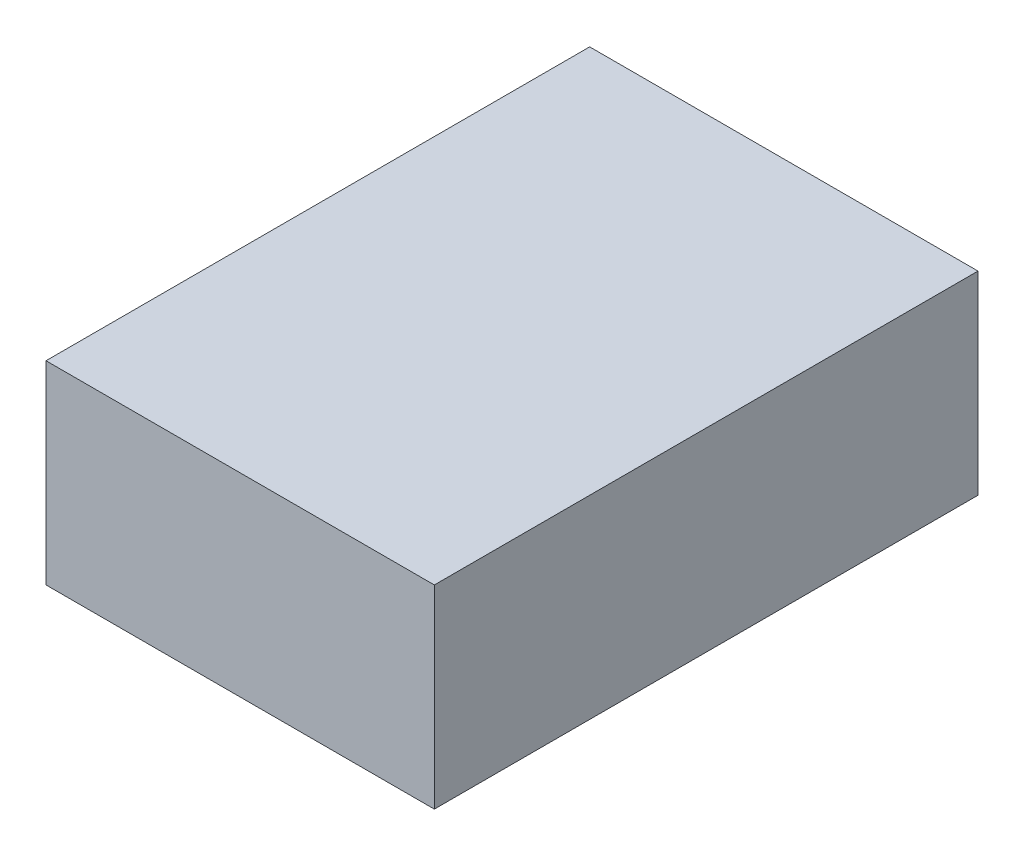
SolidWorks part; units mm, degrees
ref_plane "Front Plane" through (0, 0, 0) normal (0, 0, 1) x (1, 0, 0)
ref_plane "Top Plane" through (0, 0, 0) normal (0, 1, 0) x (1, 0, 0)
ref_plane "Right Plane" through (0, 0, 0) normal (1, 0, 0) x (0, 0, -1)
sketch "Sketch2" plane through (0, 0, 0) normal (0, 0, 1) x (1, 0, 0)
  line L1 (0, 0) -> (127, 0)
  line L2 (0, 0) -> (0, 63.5)
  line L3 (0, 63.5) -> (127, 63.5)
  line L4 (127, 0) -> (127, 63.5)
  dimension "D1" = 63.5
  dimension "D2" = 127
extrude "Boss-Extrude1" add sketch "Sketch2" along normal blind 177.8
sketch "Sketch3" plane through (0, 0, 0) normal (0, -1, 0) x (1, 0, 0)
  line L1 (0, 0) -> (92.202, 0) construction
  line L2 (0, 0) -> (0, 88.9) construction
  line L3 (0, 88.9) -> (92.202, 88.9) construction
  line L4 (92.202, 0) -> (92.202, 88.9) construction
  line L5 (0, 0) -> (88.9, 0) construction
  line L6 (0, 0) -> (0, 50.8) construction
  line L7 (0, 50.8) -> (88.9, 50.8) construction
  line L8 (88.9, 0) -> (88.9, 50.8) construction
  circle A0 centre (92.202, 88.9) radius 9.525
  circle A1 centre (88.9, 50.8) radius 6.35
  dimension "D3" = 19.05
  dimension "D6" = 12.7
  dimension "D1" = 88.9
  dimension "D2" = 92.202
  dimension "D4" = 88.9
  dimension "D5" = 50.8
sketch "Sketch6" plane through (0, 63.5, 0) normal (0, 1, 0) x (1, 0, 0)
  line L1 (0, 0) -> (88.9, 0) construction
  line L2 (0, 0) -> (0, -50.8) construction
  line L3 (0, -50.8) -> (88.9, -50.8) construction
  line L4 (88.9, 0) -> (88.9, -50.8) construction
  circle A0 centre (88.9, -50.8) radius 6.35
  dimension "D3" = 12.7
  dimension "D1" = 88.9
  dimension "D2" = 50.8
